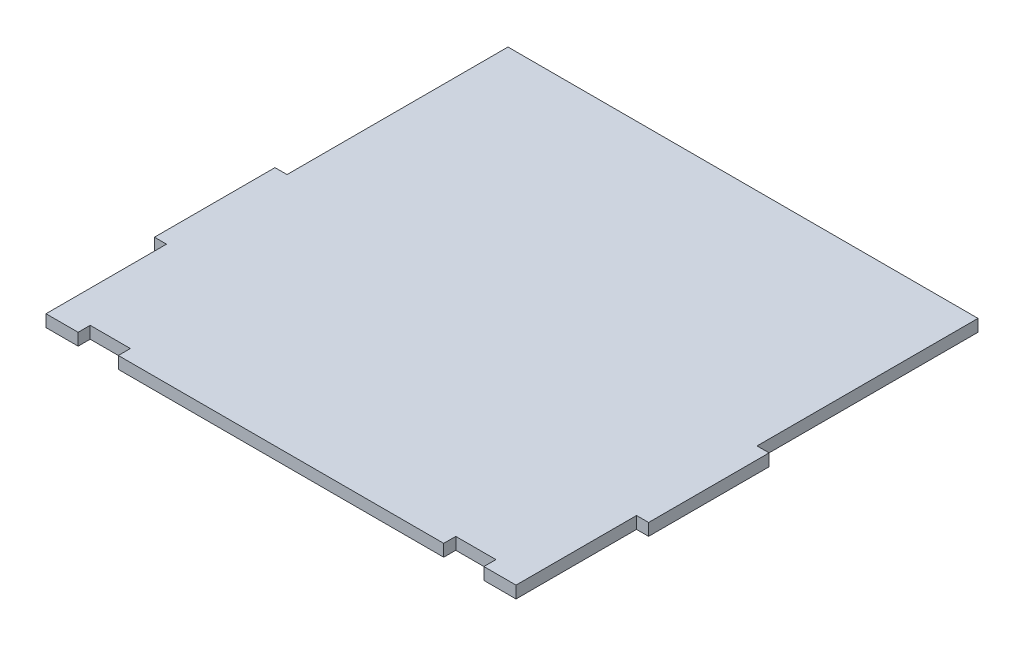
SolidWorks part; units mm, degrees
ref_plane "Front Plane" through (0, 0, 0) normal (0, 0, 1) x (1, 0, 0)
ref_plane "Top Plane" through (0, 0, 0) normal (0, 1, 0) x (1, 0, 0)
ref_plane "Right Plane" through (0, 0, 0) normal (1, 0, 0) x (0, 0, -1)
sketch "Sketch1" plane through (0, 0, 0) normal (0, 1, 0) x (1, 0, 0)
  line L0 (-50.5988, -26.8319) -> (-50.5988, 3.1681)
  line L1 (-50.5988, 3.1681) -> (-53.5988, 3.1681)
  line L2 (-53.5988, 3.1681) -> (-53.5988, 33.1681)
  line L3 (-53.5988, 33.1681) -> (-50.5988, 33.1681)
  line L4 (-50.5988, 33.1681) -> (-50.5988, 88.1681)
  line L5 (-50.5988, 88.1681) -> (66.4012, 88.1681)
  line L6 (66.4012, 88.1681) -> (66.4012, 33.1681)
  line L7 (66.4012, 33.1681) -> (69.4012, 33.1681)
  line L8 (69.4012, 33.1681) -> (69.4012, 3.1681)
  line L9 (69.4012, 3.1681) -> (66.4012, 3.1681)
  line L10 (66.4012, 3.1681) -> (66.4012, -26.8319)
  line L11 (66.4012, -26.8319) -> (8.2353, -26.8319) construction
  line L15 (-21.7647, -26.8319) -> (-50.5988, -26.8319) construction
  line L16 (-21.7647, -26.8319) -> (8.2353, -26.8319) construction
  line L17 (-50.5988, -26.8319) -> (-42.5988, -26.8319)
  line L18 (-42.5988, -26.8319) -> (-42.5988, -23.8319)
  line L19 (-42.5988, -23.8319) -> (-32.5988, -23.8319)
  line L20 (48.4012, -26.8319) -> (48.4012, -23.8319)
  line L21 (48.4012, -23.8319) -> (58.4012, -23.8319)
  line L22 (58.4012, -23.8319) -> (58.4012, -26.8319)
  line L23 (58.4012, -26.8319) -> (66.4012, -26.8319)
  line L24 (-32.5988, -23.8319) -> (-32.5988, -26.8319)
  line L25 (-32.5988, -26.8319) -> (48.4012, -26.8319)
  dimension "D2" = 3
  dimension "D3" = 10
  dimension "D4" = 55
  dimension "D5" = 30
  dimension "D6" = 117
  dimension "D7" = 3
  dimension "D8" = 3
  dimension "D9" = 10
  dimension "D10" = 3
  dimension "D11" = 3
  dimension "D12" = 8
  dimension "D13" = 8
  dimension "D14" = 30
extrude "Boss-Extrude1" add sketch "Sketch1" along normal blind 3
